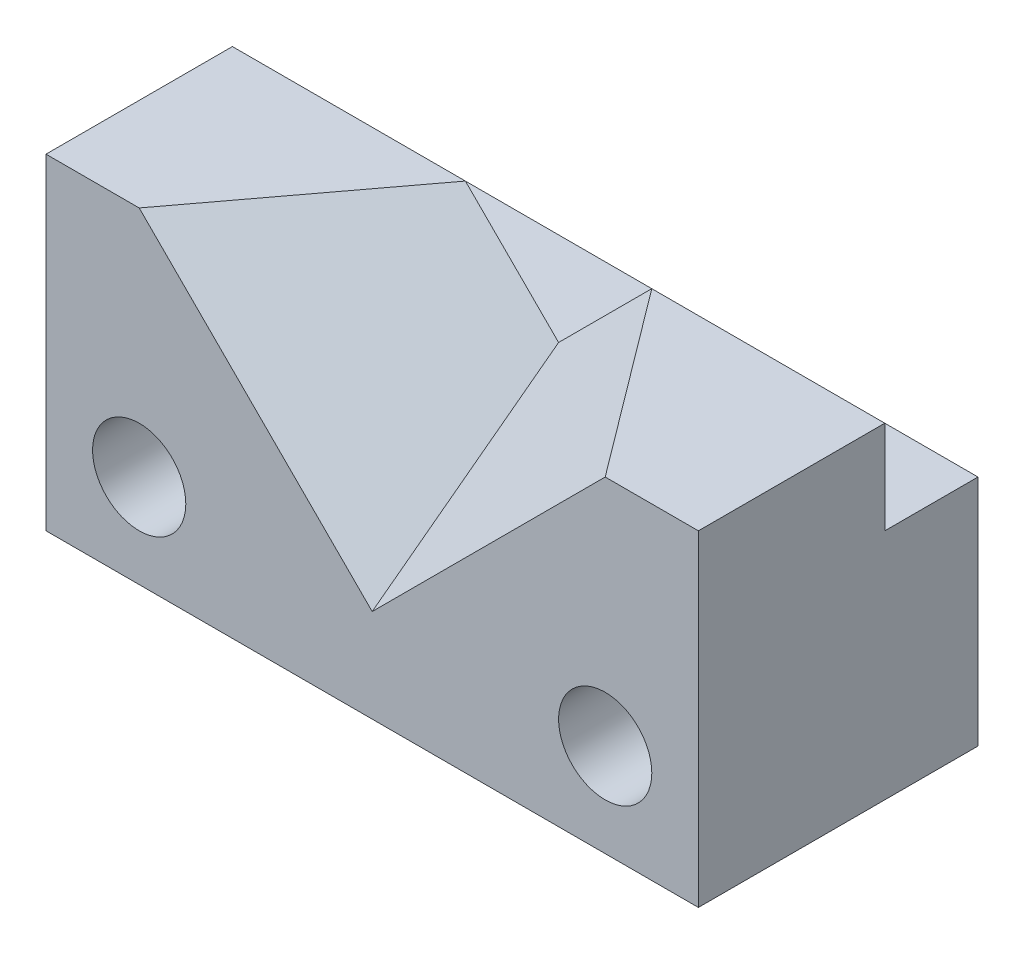
SolidWorks part; units mm, degrees
ref_plane "Front Plane" through (0, 0, 0) normal (0, 0, 1) x (1, 0, 0)
ref_plane "Top Plane" through (0, 0, 0) normal (0, 1, 0) x (1, 0, 0)
ref_plane "Right Plane" through (0, 0, 0) normal (1, 0, 0) x (0, 0, -1)
sketch "Sketch1" plane through (0, 0, 0) normal (0, 1, 0) x (1, 0, 0)
  line L1 (0, 0) -> (35, 0)
  line L2 (0, 0) -> (0, 30)
  line L3 (0, 30) -> (35, 30)
  line L4 (35, 0) -> (35, 30)
  dimension "D1" = 35
  dimension "D2" = 30
extrude "Boss-Extrude1" add sketch "Sketch1" along normal blind 35
sketch "Sketch2" plane through (0, 35, 0) normal (0, 1, 0) x (1, 0, 0)
  line L0 (35, 0) -> (35, 30) construction
  line L1 (0, 30) -> (35, 30)
  line L2 (0, 30) -> (0, 20)
  line L3 (0, 20) -> (35, 20)
  line L4 (35, 30) -> (35, 20)
  dimension "D1" = 10
extrude "Cut-Extrude1" cut sketch "Sketch2" against normal blind 10
sketch "Sketch4" plane through (0, 35, 0) normal (0, 1, 0) x (1, 0, 0)
  line L0 (0, 0) -> (10, 0) construction
  line L1 (0, 0) -> (35, 0) construction
  line L2 (35, 20) -> (25, 20) construction
  line L3 (0, 20) -> (35, 20) construction
  line L4 (10, 0) -> (25, 20)
  dimension "D1" = 10
  dimension "D2" = 10
sketch "Sketch5" plane through (0, 0, 0) normal (0, 0, 1) x (1, 0, 0)
  line L0 (35, 0) -> (35, 10) construction
  line L1 (35, 35) -> (35, 0) construction
  line L2 (10, 35) -> (35, 10)
  dimension "D1" = 10
sketch "Sketch6" plane through (35, 0, 0) normal (1, 0, 0) x (0, 0, -1)
  line L0 (0, 10) -> (20, 25)
  line L1 (0, 0) -> (0, 10) construction
sketch "Sketch7" plane through (0, 0, -20) normal (0, 0, -1) x (-1, 0, 0)
  line L0 (-35, 25) -> (-25, 35)
ref_plane "Plane1" through (17.561, 17.561, 13.1707) normal (0.6247, 0.6247, 0.4685) x (0.7809, -0.4998, -0.3748)
sketch "Sketch8" plane through (17.561, 17.561, 13.1707) normal (0.6247, 0.6247, 0.4685) x (0.7809, -0.4998, -0.3748)
  line L0 (-9.6828, 21) -> (22.3328, 6)
  line L1 (22.3328, 6) -> (22.3328, 31)
  line L2 (22.3328, 31) -> (9.5266, 37)
  line L3 (9.5266, 37) -> (-9.6828, 21)
extrude "Cut-Extrude3" cut sketch "Sketch8" along normal through all
sketch "Sketch10" plane through (0, 0, -20) normal (0, 0, -1) x (-1, 0, 0)
  line L0 (-35, 35) -> (-25, 35)
  line L1 (-25, 35) -> (-35, 25)
  line L2 (-35, 25) -> (-35, 35)
extrude "Cut-Extrude4" cut sketch "Sketch10" against normal through all
mirror "Mirror5" about plane through (35, 35, 0) normal (-1, 0, 0) of "Cut-Extrude1", "Boss-Extrude1", "Cut-Extrude3"
sketch "Sketch12" plane through (0, 0, -20) normal (0, 0, -1) x (-1, 0, 0)
  line L0 (-45, 35) -> (-35, 25)
  line L1 (-35, 25) -> (-35, 35)
  line L2 (-35, 35) -> (-25, 35) construction
  line L3 (-35, 25) -> (-35, 35) construction
  line L4 (-35, 35) -> (-45, 35)
extrude "Cut-Extrude5" cut sketch "Sketch12" against normal blind 19
sketch "Sketch13" plane through (0, 0, 0) normal (0, 0, 1) x (1, 0, 0)
  line L0 (0, 0) -> (10, 0) construction
  line L1 (0, 0) -> (70, 0) construction
  line L2 (10, 0) -> (10, 10) construction
  circle A0 centre (10, 10) radius 5
  dimension "D3" = 10
  dimension "D1" = 10
  dimension "D2" = 10
extrude "Cut-Extrude6" cut sketch "Sketch13" against normal through all contours A0
sketch "Sketch14" plane through (0, 0, 0) normal (0, 0, 1) x (1, 0, 0)
  line L0 (70, 0) -> (60, 0) construction
  line L1 (0, 0) -> (70, 0) construction
  line L2 (60, 0) -> (60, 10) construction
  circle A0 centre (60, 10) radius 5
  dimension "D3" = 10
  dimension "D1" = 10
  dimension "D2" = 10
extrude "Cut-Extrude7" cut sketch "Sketch14" against normal through all contours A0
